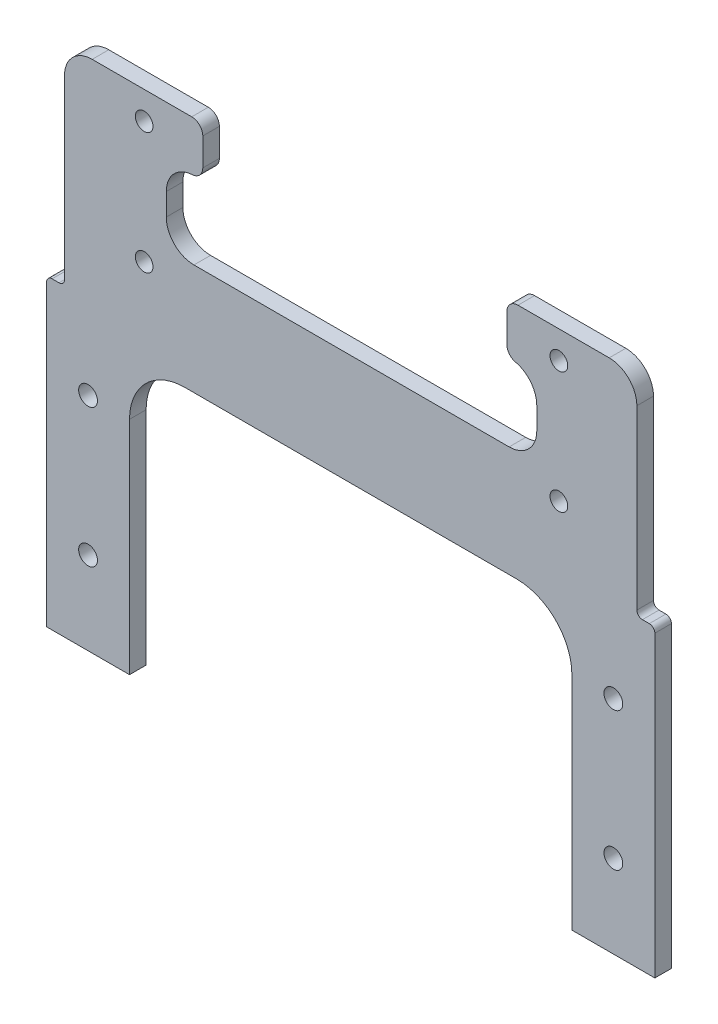
SolidWorks part; units mm, degrees
material "A-玻璃纤维"
ref_plane "前视基准面" through (0, 0, 0) normal (0, 0, 1) x (1, 0, 0)
ref_plane "上视基准面" through (0, 0, 0) normal (0, 1, 0) x (1, 0, 0)
ref_plane "右视基准面" through (0, 0, 0) normal (1, 0, 0) x (0, 0, -1)
sketch "草图1" plane through (0, 0, 0) normal (0, 0, 1) x (1, 0, 0)
  line L0 (0, 0) -> (0, 33.113) construction
  line L1 (-47.5, 12.5) -> (47.5, 12.5) construction
  line L2 (-47.5, 12.5) -> (-47.5, -12.5) construction
  line L3 (-47.5, -12.5) -> (47.5, -12.5) construction
  line L4 (47.5, 12.5) -> (47.5, -12.5) construction
  line L5 (-47.5, 12.5) -> (47.5, -12.5) construction
  line L6 (-47.5, -12.5) -> (47.5, 12.5) construction
  line L8 (-55, 27.5) -> (55, 27.5)
  line L9 (-55, 27.5) -> (-55, -27.5)
  line L10 (-55, -27.5) -> (55, -27.5)
  line L11 (55, 27.5) -> (55, -27.5)
  line L12 (-55, 27.5) -> (55, -27.5) construction
  line L13 (-55, -27.5) -> (55, 27.5) construction
  circle A0 centre (-47.5, 12.5) radius 1.7
  circle A1 centre (-47.5, -12.5) radius 1.7
  circle A2 centre (47.5, 12.5) radius 1.7
  circle A3 centre (47.5, -12.5) radius 1.7
  point P0 (0, 0)
  dimension "D1" = 3.4
  dimension "D2" = 95
  dimension "D3" = 25
  dimension "D4" = 110
  dimension "D5" = 55
extrude "凸台-拉伸1" add sketch "草图1" along normal blind 3
sketch "草图2" plane through (0, 0, 3) normal (0, 0, 1) x (1, 0, 0)
  line L0 (-51.75, 27.5) -> (-51.75, 65.5)
  line L1 (55, 27.5) -> (-55, 27.5) construction
  line L2 (-51.75, 65.5) -> (51.75, 65.5)
  line L3 (51.75, 65.5) -> (51.75, 27.5)
  line L4 (0, 0) -> (0, 44.9366) construction
  line L6 (51.75, 27.5) -> (-51.75, 27.5)
  dimension "D1" = 103.5
  dimension "D2" = 38
extrude "凸台-拉伸2" add sketch "草图2" against normal blind 3
sketch "草图3" plane through (0, 0, 0) normal (0, 0, -1) x (-1, 0, 0)
  line L0 (-51.75, 65.5) -> (51.75, 65.5) construction
  line L1 (51.75, 65.5) -> (51.75, 27.5) construction
  circle A0 centre (37.35, 60.5) radius 1.6
  circle A1 centre (-37.65, 60.5) radius 1.6
  circle A2 centre (-37.65, 38.5) radius 1.6
  circle A3 centre (37.35, 38.5) radius 1.6
  dimension "D1" = 3.2
  dimension "D2" = 5
  dimension "D3" = 14.4
  dimension "D4" = 75
  dimension "D5" = 22
  dimension "D6" = 22
extrude "切除-拉伸1" cut sketch "草图3" against normal through all
sketch "草图4" plane through (0, 0, 3) normal (0, 0, 1) x (1, 0, 0)
  line L0 (-40, -27.5) -> (-40, 22.5)
  line L1 (-55, -27.5) -> (55, -27.5) construction
  line L2 (-40, 22.5) -> (40, 22.5)
  line L3 (40, 22.5) -> (40, -27.5)
  line L4 (40, -27.5) -> (-40, -27.5)
  line L5 (0, 0) -> (0, -36.1832) construction
  line L6 (-55, 27.5) -> (-55, -27.5) construction
  line L7 (-37.35, 60.5) -> (-37.35, 38.5) construction
  line L8 (-37.35, 38.5) -> (37.65, 38.5) construction
  line L9 (37.65, 38.5) -> (37.65, 60.5) construction
  line L10 (37.65, 60.5) -> (-37.35, 60.5) construction
  line L11 (-33.35, 56.5) -> (-33.35, 42.5)
  line L12 (-33.35, 42.5) -> (33.65, 42.5)
  line L13 (33.65, 42.5) -> (33.65, 56.5)
  line L14 (33.65, 56.5) -> (-33.35, 56.5)
  dimension "D1" = 15
  dimension "D2" = 50
  dimension "D3" = 4
extrude "切除-拉伸2" cut sketch "草图4" against normal through all
fillet "圆角2" radius 10 2 edges at (40, 22.5, 1.5) (-40, 22.5, 1.5)
fillet "圆角3" radius 1 4 edges at (55, 27.5, 1.5) (51.75, 27.5, 1.5) (-55, 27.5, 1.5) (-51.75, 27.5, 1.5)
sketch "草图6" plane through (0, 0, 3) normal (0, 0, 1) x (1, 0, 0)
  line L0 (-51.75, 65.5) -> (-51.75, 85.5)
  line L1 (-51.75, 85.5) -> (51.75, 85.5)
  line L2 (0, 0) -> (0, 85.5) construction
  line L3 (-37.35, 60.5) -> (-37.35, 75.2) construction
  line L4 (51.75, 65.5) -> (-51.75, 65.5) construction
  line L5 (51.75, 65.5) -> (51.75, 85.5)
  line L6 (-51.75, 65.5) -> (51.75, 65.5)
  dimension "D2" = 20
  dimension "D1" = 14.7
extrude "凸台-拉伸3" [suppressed] add sketch "草图6" against normal up to surface (3 mm away)
sketch "草图7" plane through (0, 0, 3) normal (0, 0, 1) x (1, 0, 0)
  line L0 (-37.35, 60.5) -> (-37.35, 75.2) construction
  line L1 (-37.35, 38.5) -> (-37.35, 53.2) construction
  line L2 (0, 0) -> (0, 70) construction
  line L4 (33.65, 42.5) -> (33.65, 56.5) construction
  line L5 (-33.65, 61.5) -> (33.65, 61.5)
  line L6 (-33.65, 61.5) -> (-33.65, 78.5)
  line L7 (-33.65, 78.5) -> (33.65, 78.5)
  line L8 (33.65, 61.5) -> (33.65, 78.5)
  line L9 (-33.65, 61.5) -> (33.65, 78.5) construction
  line L10 (-33.65, 78.5) -> (33.65, 61.5) construction
  line L11 (33.65, 56.5) -> (-33.35, 56.5) construction
  circle A0 centre (-37.35, 75.2) radius 1.65
  circle A1 centre (-37.35, 53.2) radius 1.65
  circle A2 centre (37.35, 53.2) radius 1.65
  circle A3 centre (37.35, 75.2) radius 1.65
  dimension "D2" = 3.3
  dimension "D4" = 3.3
  dimension "D1" = 14.7
  dimension "D3" = 14.7
  dimension "D5" = 5
  dimension "D6" = 17
extrude "切除-拉伸3" [suppressed] cut sketch "草图7" against normal through all
fillet "圆角4" [suppressed] radius 3
sketch "草图8" [suppressed] plane through (0, 0, 3) normal (0, 0, 1) x (1, 0, 0)
  line L5 (-33.35, 34.5) -> (-33.65, 50.5)
  line L6 (-33.65, 50.5) -> (33.65, 50.5)
  line L8 (33.65, 50.5) -> (33.65, 34.5)
  line L9 (33.65, 34.5) -> (-33.35, 34.5)
extrude "切除-拉伸4" [suppressed] cut sketch "草图8" against normal blind 10
sketch "草图9" plane through (0, 0, 3) normal (0, 0, 1) x (1, 0, 0)
  circle A0 centre (-37.35, 38.5) radius 1.6 construction
  circle A1 centre (-37.35, 60.5) radius 1.6 construction
  circle A2 centre (-37.35, 38.5) radius 1.6
  circle A3 centre (-37.35, 60.5) radius 1.6
  circle A4 centre (37.65, 38.5) radius 1.6 construction
  circle A5 centre (37.65, 60.5) radius 1.6 construction
  circle A6 centre (37.65, 38.5) radius 1.6
  circle A7 centre (37.65, 60.5) radius 1.6
extrude "凸台-拉伸4" [suppressed] add sketch "草图9" against normal up to surface (3 mm away)
fillet "圆角5" radius 5 6 edges at (33.65, 56.5, 1.5) (-33.35, 56.5, 1.5) (-33.35, 42.5, 1.5) (33.65, 42.5, 1.5) (51.75, 65.5, 1.5) (-51.75, 65.5, 1.5)
sketch "草图10" plane through (0, 0, 3) normal (0, 0, 1) x (1, 0, 0)
  line L0 (-37.35, 60.5) -> (37.65, 60.5) construction
  circle A0 centre (-22.85, 60.5) radius 1.65
  circle A1 centre (5.15, 60.5) radius 1.65
  circle A2 centre (-37.35, 60.5) radius 1.6 construction
  dimension "D1" = 3.3
  dimension "D2" = 14.5
  dimension "D3" = 28
extrude "切除-拉伸5" cut sketch "草图10" against normal through all
sketch "草图11" plane through (0, 0, 3) normal (0, 0, 1) x (1, 0, 0)
  line L0 (46.75, 65.5) -> (-46.75, 65.5) construction
  line L1 (28.25, 65.5) -> (-26.75, 65.5)
  line L2 (28.65, 56.5) -> (-28.35, 56.5) construction
  line L3 (28.25, 56.5) -> (-26.75, 56.5)
  line L4 (-26.75, 56.5) -> (-26.75, 65.5)
  line L5 (28.25, 56.5) -> (28.25, 65.5)
  line L6 (-51.75, 60.5) -> (-51.75, 28.5) construction
  dimension "D1" = 55
  dimension "D2" = 25
extrude "切除-拉伸6" cut sketch "草图11" against normal through all
fillet "圆角6" radius 2 4 edges at (28.25, 56.5, 1.5) (28.25, 65.5, 1.5) (-26.75, 56.5, 1.5) (-26.75, 65.5, 1.5)
